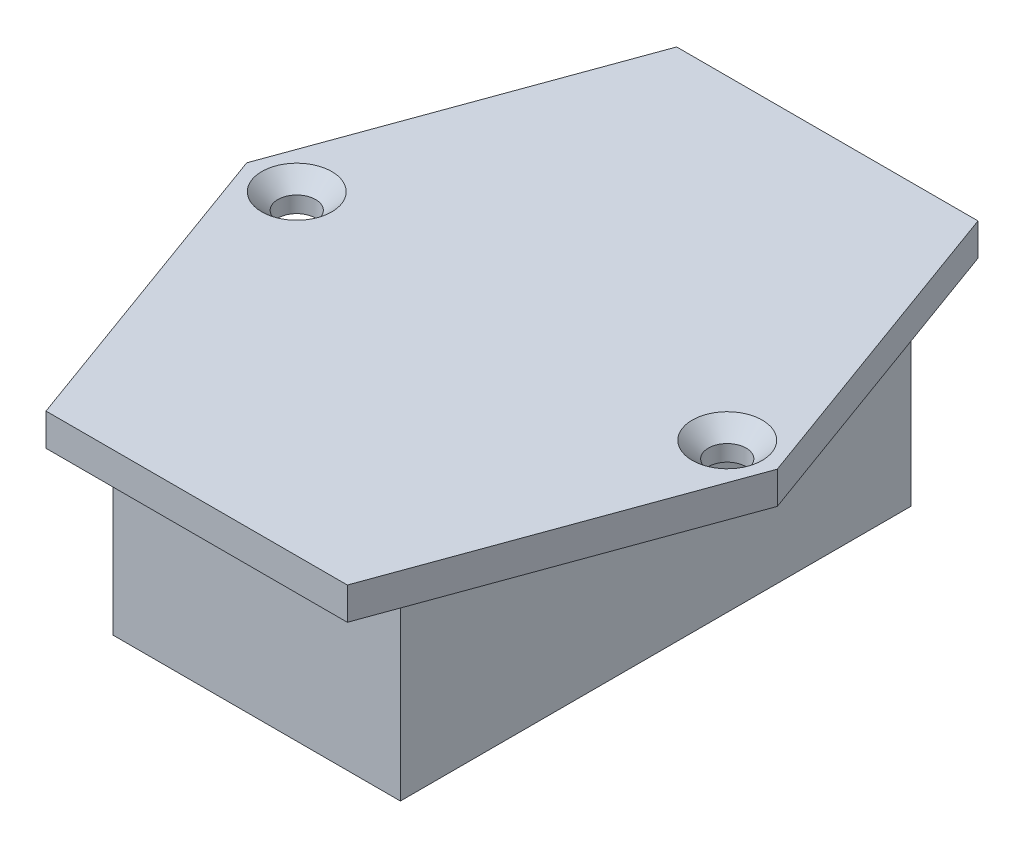
SolidWorks part; units mm, degrees
ref_plane "Front Plane" through (0, 0, 0) normal (0, 0, 1) x (1, 0, 0)
ref_plane "Top Plane" through (0, 0, 0) normal (0, 1, 0) x (1, 0, 0)
ref_plane "Right Plane" through (0, 0, 0) normal (1, 0, 0) x (0, 0, -1)
sketch "Sketch1" plane through (0, 0, 0) normal (0, 1, 0) x (1, 0, 0)
  line L0 (0, 0) -> (-24.65, 0) construction
  line L1 (0, 0) -> (0, 29.3) construction
  line L2 (14, 29.3) -> (-14, 29.3)
  line L3 (-14, 29.3) -> (-24.65, 0)
  line L4 (14, 29.3) -> (24.65, 0)
  line L5 (14, -29.3) -> (24.65, 0)
  line L6 (14, -29.3) -> (-14, -29.3)
  line L7 (-14, -29.3) -> (-24.65, 0)
  dimension "D1" = 24.65
  dimension "D2" = 29.3
  dimension "D3" = 14
extrude "Boss-Extrude1" add sketch "Sketch1" along normal blind 3
sketch "Sketch2" plane through (0, 0, 0) normal (0, -1, 0) x (1, 0, 0)
  line L1 (13.35, 23.72) -> (-13.35, 23.72)
  line L2 (13.35, 23.72) -> (13.35, -23.72)
  line L3 (13.35, -23.72) -> (-13.35, -23.72)
  line L4 (-13.35, 23.72) -> (-13.35, -23.72)
  line L5 (13.35, 23.72) -> (-13.35, -23.72) construction
  line L6 (13.35, -23.72) -> (-13.35, 23.72) construction
  point P0 (0, 0)
  dimension "D1" = 47.44
  dimension "D2" = 26.7
extrude "Boss-Extrude2" add sketch "Sketch2" along normal blind 17.5
sketch "Sketch3" plane through (0, -17.5, 0) normal (0, -1, 0) x (1, 0, 0)
  line L0 (0, 0) -> (0, -23.72) construction
  line L1 (-13.35, -23.72) -> (13.35, -23.72) construction
  line L3 (2.5, -19.47) -> (-2.5, -19.47)
  line L4 (2.5, -19.47) -> (2.5, -20.22)
  line L5 (2.5, -20.22) -> (-2.5, -20.22)
  line L6 (-2.5, -19.47) -> (-2.5, -20.22)
  line L7 (2.5, -19.47) -> (-2.5, -20.22) construction
  line L8 (2.5, -20.22) -> (-2.5, -19.47) construction
  point P5 (0, -19.845)
  dimension "D1" = 0.75
  dimension "D2" = 3.5
  dimension "D3" = 5
extrude "Boss-Extrude3" add sketch "Sketch3" along normal blind 10 separate body
sketch "Sketch4" plane through (0, 3, 0) normal (0, 1, 0) x (1, 0, 0)
  line L0 (0, -29.3) -> (0, 29.3) construction
  line L1 (-14, -29.3) -> (14, -29.3) construction
  line L2 (14, 29.3) -> (-14, 29.3) construction
  line L3 (24.65, 0) -> (-24.65, 0) construction
  circle A0 centre (20, 0) radius 1.75
  circle A1 centre (-20, 0) radius 1.75
  dimension "D1" = 3.5
  dimension "D2" = 20
extrude "Cut-Extrude1" cut sketch "Sketch4" against normal up to next (3 mm away)
chamfer "Chamfer1" distance 1.5 angle 45 2 edges at (-20, 3, -1.75) (20, 3, 1.75)
